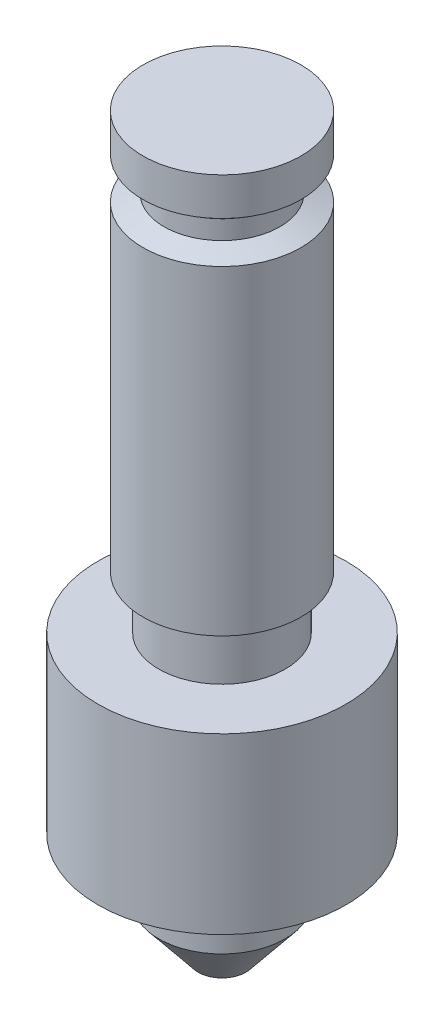
SolidWorks part; units mm, degrees
ref_plane "Front Plane" through (0, 0, 0) normal (0, 0, 1) x (1, 0, 0)
ref_plane "Top Plane" through (0, 0, 0) normal (0, 1, 0) x (1, 0, 0)
ref_plane "Right Plane" through (0, 0, 0) normal (1, 0, 0) x (0, 0, -1)
sketch "Sketch1" plane through (0, 0, 0) normal (0, 0, 1) x (1, 0, 0)
  line L0 (0, 0) -> (0, 14.2773) construction
  line L1 (0, 0) -> (-7.9629, 0)
  line L2 (-7.9629, 0) -> (-7.9629, -3.81)
  line L3 (-7.9629, -3.81) -> (-5.842, -5.334)
  line L4 (-5.842, -5.334) -> (-5.842, -7.239)
  line L5 (-5.842, -7.239) -> (-7.9629, -8.001)
  line L6 (-7.9629, -8.001) -> (-7.9629, -40.259)
  line L7 (-7.9629, -40.259) -> (-6.3754, -40.259)
  line L8 (-6.3754, -40.259) -> (-6.3754, -45.593)
  line L9 (-12.5, -63.119) -> (-6.3754, -63.119)
  line L10 (-6.3754, -63.119) -> (-6.3754, -69.1422)
  line L11 (-6.3754, -69.1422) -> (-2.4106, -74.041)
  line L12 (-2.4106, -74.041) -> (0, -74.041)
  line L13 (-6.3754, -45.593) -> (-12.5, -45.593)
  line L14 (-12.5, -45.593) -> (-12.5, -63.119)
  line L15 (0, 0) -> (0, -74.041)
  dimension "D1" = 15.9258
  dimension "D2" = 11.684
  dimension "D3" = 3.81
  dimension "D4" = 0.762
  dimension "D5" = 4.191
  dimension "D6" = 1.524
  dimension "D7" = 17.526
  dimension "D8" = 12.7508
  dimension "D9" = 10.922
  dimension "D10" = 74.041
  dimension "D11" = 32.258
  dimension "D12" = 25
revolve "Revolve1" add sketch "Sketch1" angle 360 about L0
